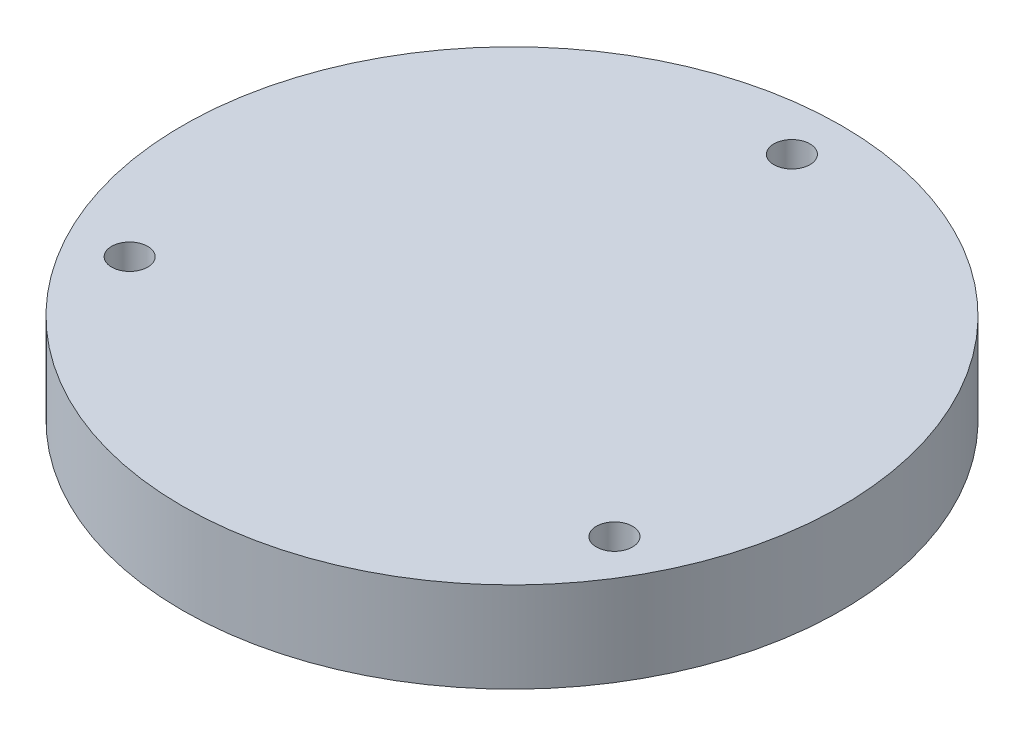
SolidWorks part; units mm, degrees
material "Acrylic (Medium-high impact)"
ref_plane "Front Plane" through (0, 0, 0) normal (0, 0, 1) x (1, 0, 0)
ref_plane "Top Plane" through (0, 0, 0) normal (0, 1, 0) x (1, 0, 0)
ref_plane "Right Plane" through (0, 0, 0) normal (1, 0, 0) x (0, 0, -1)
sketch "Sketch1" plane through (0, 0, 0) normal (0, 1, 0) x (1, 0, 0)
  circle A0 centre (0, 0) radius 36.5
  dimension "D1" = 73
extrude "Boss-Extrude1" add sketch "Sketch1" along normal blind 10
sketch "Sketch3" plane through (0, 10, 0) normal (0, 1, 0) x (1, 0, 0)
  circle A0 centre (0, 31) radius 2
  circle A1 centre (0, 0) radius 36.5 construction
  circle A2 centre (26.8468, -15.5) radius 2
  circle A3 centre (-26.8468, -15.5) radius 2
  point P12 (0, 0)
  dimension "D1" = 31
  dimension "D2" = 4
  dimension "D6" = 15.5
  dimension "D3" = 31
  dimension "D5" = 15.5
  dimension "D4" = 3
extrude "Cut-Extrude1" cut sketch "Sketch3" against normal through all
